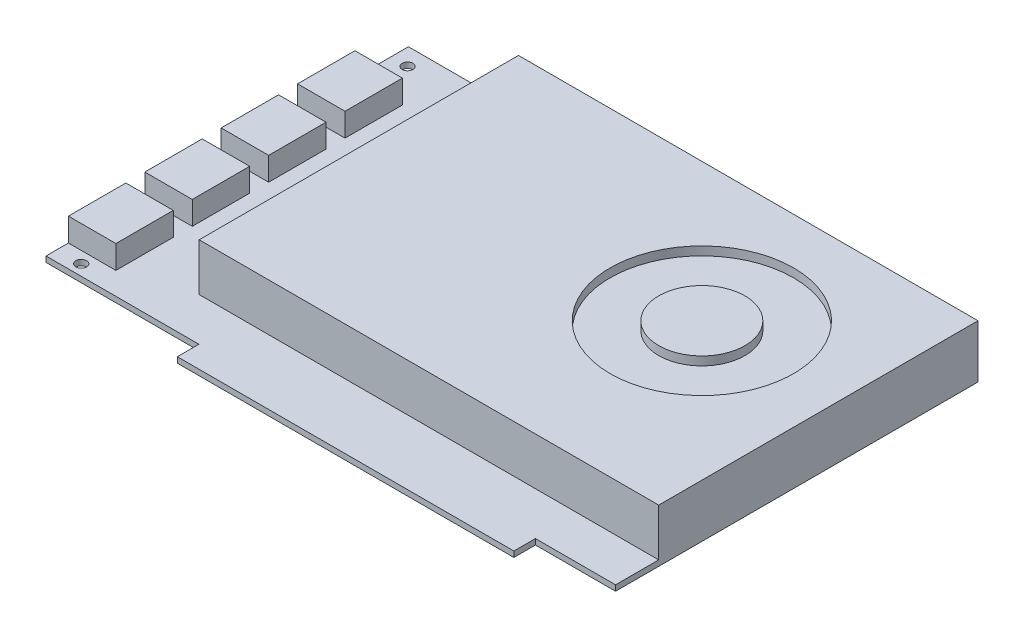
SolidWorks part; units mm, degrees
ref_plane "Front Plane" through (0, 0, 0) normal (0, 0, 1) x (1, 0, 0)
ref_plane "Top Plane" through (0, 0, 0) normal (0, 1, 0) x (1, 0, 0)
ref_plane "Right Plane" through (0, 0, 0) normal (1, 0, 0) x (0, 0, -1)
sketch "Sketch1" plane through (0, 0, 0) normal (0, 1, 0) x (1, 0, 0)
  line L0 (-38.82, -53.34) -> (-38.82, -59.69)
  line L1 (-83.82, 53.34) -> (83.82, 53.34)
  line L2 (-83.82, 53.34) -> (-83.82, -53.34)
  line L3 (-83.82, -53.34) -> (83.82, -53.34)
  line L4 (83.82, 53.34) -> (83.82, -53.34)
  line L5 (-83.82, 53.34) -> (83.82, -53.34) construction
  line L6 (-83.82, -53.34) -> (83.82, 53.34) construction
  line L7 (-38.82, -59.69) -> (60.24, -59.69)
  line L8 (60.24, -59.69) -> (60.24, -53.34)
  point P0 (0, 0)
  dimension "D1" = 167.64
  dimension "D2" = 106.68
  dimension "D3" = 45
  dimension "D4" = 6.35
  dimension "D5" = 99.06
extrude "Boss-Extrude1" add sketch "Sketch1" along normal blind 1.651 contours L4 L1 L2 L3 | L7 L8 L3 L0
sketch "Sketch2" plane through (0, 1.651, 0) normal (0, 1, 0) x (1, 0, 0)
  line L1 (83.82, 53.34) -> (-51.435, 53.34)
  line L2 (83.82, 53.34) -> (83.82, -40.64)
  line L3 (83.82, -40.64) -> (-51.435, -40.64)
  line L4 (-51.435, 53.34) -> (-51.435, -40.64)
  dimension "D1" = 93.98
  dimension "D2" = 135.255
extrude "Boss-Extrude2" add sketch "Sketch2" along normal blind 13.97
sketch "Sketch4" plane through (0, 1.651, 0) normal (0, 1, 0) x (1, 0, 0)
  line L0 (-83.82, 53.34) -> (-83.82, -53.34) construction
  line L1 (-83.82, 53.34) -> (-51.435, 53.34) construction
  point P0 (-78.9305, 48.1965)
  point P5 (-76.6445, -50.1523)
  point P6 (-67.6275, 53.34)
  dimension "D1" = 4.8895
  dimension "D2" = 5.1435
  dimension "D3" = 7.1755
  dimension "D4" = 103.4923
hole_wizard "#4 Clearance Hole1" positions "3DSketch1" profile "Sketch5" hole size "#4" standard "ANSI Inch" end condition through all
sketch3d "3DSketch1"
  point P0 (-78.9305, 1.651, -48.1965)
  point P3 (-76.6445, 1.651, 50.1523)
sketch "Sketch5" plane through (-78.9305, 1.651, -48.1965) normal (1, 0, 0) x (0, 0, 1)
  line L0 (0, 0) -> (0, 1.651)
  line L1 (0, 1.651) -> (1.5875, 1.651)
  line L2 (1.5875, 1.651) -> (1.5875, 0)
  line L5 (1.5875, 0) -> (0, 0)
  line L11 (0, -6.35) -> (0, 107.95) construction
  dimension "Thru Hole Dia." = 3.175
  dimension "Thru Hole Depth" = 1.651
sketch "Sketch6" plane through (0, 1.651, 0) normal (0, 1, 0) x (1, 0, 0)
  line L0 (-83.82, 53.34) -> (-83.82, -53.34) construction
  line L1 (-83.82, 37.592) -> (-69.85, 37.592)
  line L2 (-83.82, 37.592) -> (-83.82, 20.701)
  line L3 (-83.82, 20.701) -> (-69.85, 20.701)
  line L4 (-69.85, 37.592) -> (-69.85, 20.701)
  line L5 (-83.82, 53.34) -> (-51.435, 53.34) construction
  line L6 (-83.82, 15.113) -> (-69.85, 15.113)
  line L7 (-83.82, 15.113) -> (-83.82, -1.778)
  line L8 (-83.82, -1.778) -> (-69.85, -1.778)
  line L9 (-69.85, 15.113) -> (-69.85, -1.778)
  line L10 (-83.82, -7.366) -> (-69.85, -7.366)
  line L11 (-83.82, -7.366) -> (-83.82, -24.257)
  line L12 (-83.82, -24.257) -> (-69.85, -24.257)
  line L13 (-69.85, -7.366) -> (-69.85, -24.257)
  line L14 (-83.82, -29.845) -> (-69.85, -29.845)
  line L15 (-83.82, -29.845) -> (-83.82, -46.736)
  line L16 (-83.82, -46.736) -> (-69.85, -46.736)
  line L17 (-69.85, -29.845) -> (-69.85, -46.736)
  line L18 (-83.82, 37.592) -> (-83.82, 15.113) construction
  point P6 (-69.85, 29.1465)
  dimension "D1" = 13.97
  dimension "D2" = 16.891
  dimension "D3" = 15.748
  dimension "D5" = 5.588
  dimension "D4" = 4
extrude "Boss-Extrude3" add sketch "Sketch6" along normal blind 6.858
sketch "Sketch7" plane through (-51.435, 0, 0) normal (-1, 0, 0) x (0, 0, 1)
  line L0 (40.64, 8.636) -> (-53.34, 8.636) construction
  line L2 (35.56, 14.986) -> (38.1, 14.986)
  line L3 (35.56, 14.986) -> (35.56, 2.286)
  line L4 (-53.34, 1.651) -> (40.64, 1.651)
  line L5 (40.64, 1.651) -> (40.64, 15.621)
  line L6 (40.64, 15.621) -> (-53.34, 15.621)
  line L7 (-53.34, 15.621) -> (-53.34, 1.651)
  line L8 (-53.34, 1.651) -> (40.64, 1.651)
  line L9 (40.64, 1.651) -> (40.64, 15.621)
  line L10 (40.64, 15.621) -> (-53.34, 15.621)
  line L11 (-53.34, 15.621) -> (-53.34, 1.651)
  line L12 (35.56, 2.286) -> (38.1, 2.286)
  line L13 (38.1, 14.986) -> (38.1, 2.286)
  line L14 (35.56, 14.986) -> (38.1, 2.286) construction
  line L15 (35.56, 2.286) -> (38.1, 14.986) construction
  point P6 (36.83, 8.636)
  dimension "D2" = 12.7
  dimension "D3" = 2.54
  dimension "D4" = 2.54
  dimension "D1" = 0
extrude "Cut-Extrude5" cut sketch "Sketch7" against normal blind 2.54 contours L13 L2 L3 L12
pattern_linear "LPattern1" count 18 spacing 5.08 along (0, 0, -1) of "Cut-Extrude5"
sketch "Sketch8" plane through (0, 15.621, 0) normal (0, 1, 0) x (1, 0, 0)
  line L0 (83.82, -40.64) -> (83.82, 53.34) construction
  line L1 (83.82, 53.34) -> (-51.435, 53.34) construction
  circle A0 centre (43.18, 12.7) radius 26.9875
  circle A1 centre (43.18, 12.7) radius 12.7
  dimension "D3" = 53.975
  dimension "D4" = 25.4
  dimension "D1" = 40.64
  dimension "D2" = 40.64
extrude "Cut-Extrude6" cut sketch "Sketch8" against normal blind 2.54
ref_plane "Plane1" through (0, 0.8255, 0) normal (0, -1, 0) x (-1, 0, 0)
